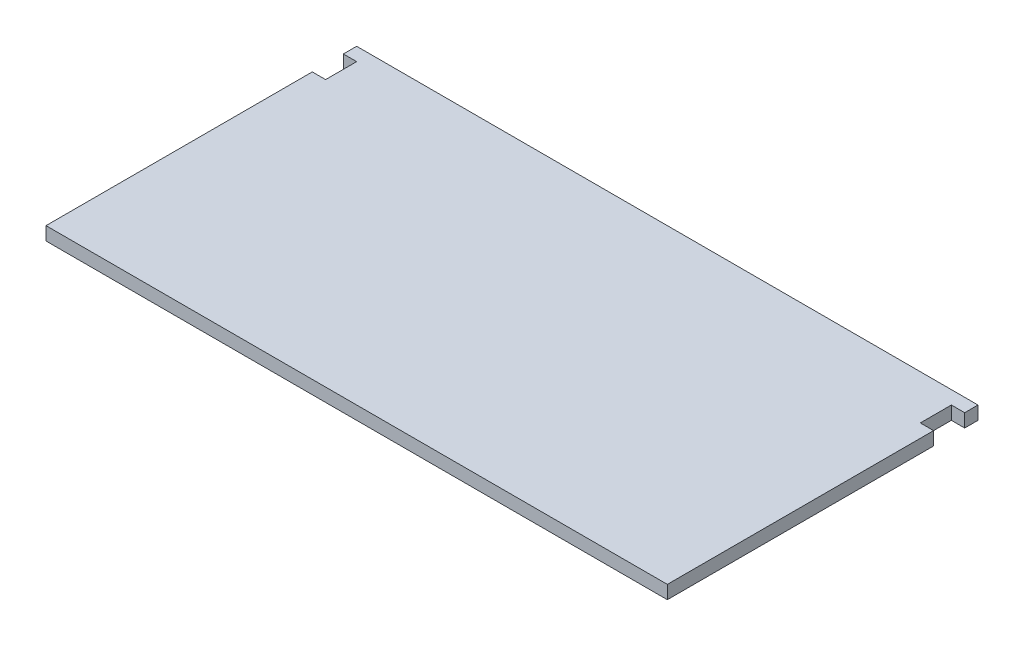
SolidWorks part; units mm, degrees
ref_plane "Front Plane" through (0, 0, 0) normal (0, 0, 1) x (1, 0, 0)
ref_plane "Top Plane" through (0, 0, 0) normal (0, 1, 0) x (1, 0, 0)
ref_plane "Right Plane" through (0, 0, 0) normal (1, 0, 0) x (0, 0, -1)
sketch "Sketch1" plane through (0, 0, 0) normal (0, 1, 0) x (1, 0, 0)
  line L1 (-70, -35) -> (70, -35)
  line L2 (-70, -35) -> (-70, 35)
  line L3 (-70, 35) -> (70, 35)
  line L4 (70, -35) -> (70, 35)
  line L5 (-70, -35) -> (70, 35) construction
  line L6 (-70, 35) -> (70, -35) construction
  point P0 (0, 0)
  dimension "D1" = 140
  dimension "D2" = 70
extrude "Boss-Extrude1" add sketch "Sketch1" along normal blind 3
sketch "Sketch2" plane through (0, 3, 0) normal (0, 1, 0) x (1, 0, 0)
  line L0 (-70, 32) -> (-67, 32)
  line L1 (-70, 35) -> (-70, -35) construction
  line L2 (-67, 32) -> (-67, 25)
  line L3 (-67, 25) -> (-70, 25)
  line L4 (-70, 25) -> (-70, 32)
  line L5 (70, 35) -> (-70, 35) construction
  line L6 (0, -1.65) -> (0, 1.65) construction
  line L7 (67, 25) -> (70, 25)
  line L8 (67, 32) -> (67, 25)
  line L9 (70, 32) -> (67, 32)
  line L10 (70, 25) -> (70, 32)
  dimension "D1" = 7
  dimension "D2" = 3
  dimension "D3" = 3
extrude "Cut-Extrude1" cut sketch "Sketch2" against normal blind 3
ref_plane "Plane1" through (0, 1.5, 0) normal (0, -1, 0) x (-1, 0, 0)
sketch "Sketch3" plane through (0, 1.5, 0) normal (0, -1, 0) x (-1, 0, 0)
  line L1 (-70, 32) -> (-70, 35) construction
  line L2 (70, 33.5) -> (-70, 33.5) construction
  line L3 (70, 35) -> (70, 32) construction
